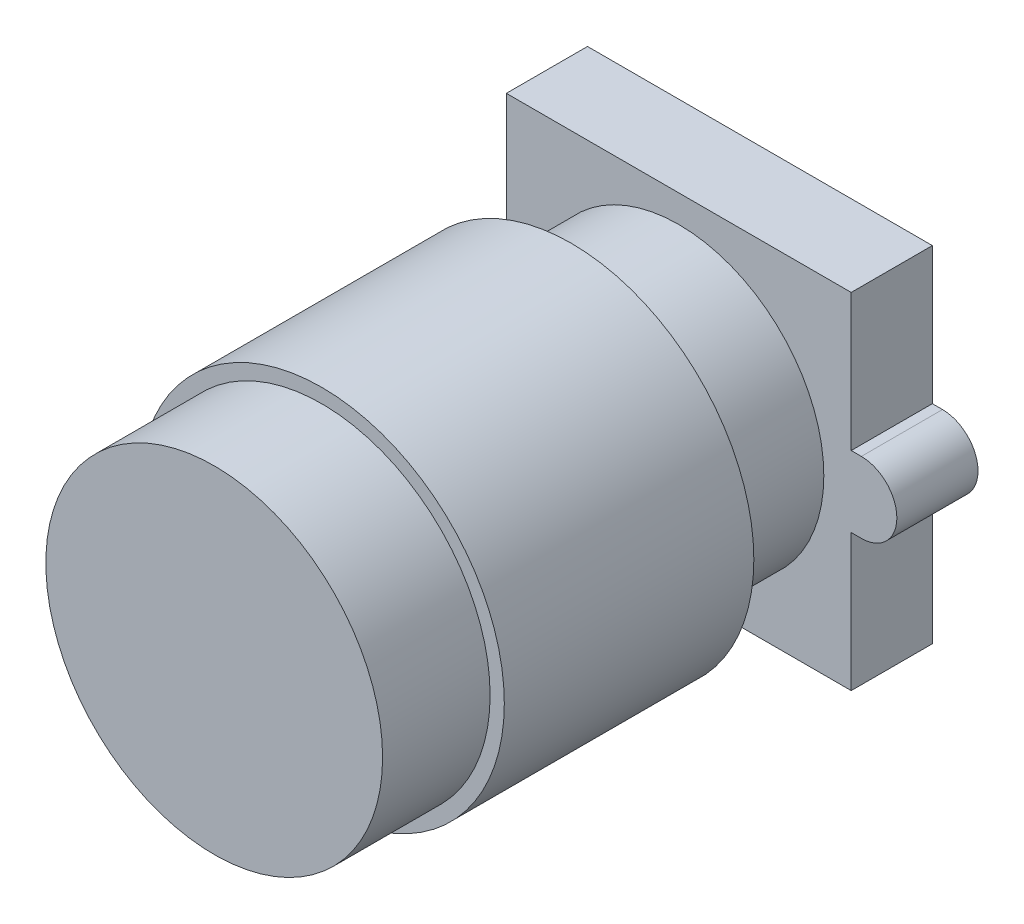
SolidWorks part; units mm, degrees
ref_plane "Front Plane" through (0, 0, 0) normal (0, 0, 1) x (1, 0, 0)
ref_plane "Top Plane" through (0, 0, 0) normal (0, 1, 0) x (1, 0, 0)
ref_plane "Right Plane" through (0, 0, 0) normal (1, 0, 0) x (0, 0, -1)
sketch "Sketch2" plane through (0, 0, 0) normal (0, 0, 1) x (1, 0, 0)
  line L0 (-9, 0) -> (9, 0) construction
  line L1 (8.5, -8.5) -> (-8.5, -8.5)
  line L2 (8.5, -8.5) -> (8.5, 8.5)
  line L3 (8.5, 8.5) -> (-8.5, 8.5)
  line L4 (-8.5, -8.5) -> (-8.5, 8.5)
  line L5 (8.5, -8.5) -> (-8.5, 8.5) construction
  line L6 (8.5, 8.5) -> (-8.5, -8.5) construction
  line L7 (-9, 1.75) -> (9, 1.75)
  line L8 (-9, -1.75) -> (9, -1.75)
  arc A0 (-9, 1.75) -> (-9, -1.75) centre (-9, 0) ccw
  arc A1 (9, -1.75) -> (9, 1.75) centre (9, 0) ccw
  point P0 (0, 0)
  point P8 (0, 0)
  point P13 (0, 0)
  dimension "D3" = 21.5
  dimension "D4" = 1.75
  dimension "D1" = 17
  dimension "D2" = 17
extrude "Boss-Extrude1" add sketch "Sketch2" along normal blind 4 contours L4 L8 L2 L7 | L7 A0 L8 L4 | L4 L7 L2 L3 | L8 L4 L1 L2 | L8 A1 L7 L2
sketch "Sketch3" plane through (0, 0, 4) normal (0, 0, 1) x (1, 0, 0)
  circle A0 centre (0, 0) radius 7.15
  point P3 (0, 0)
  dimension "D1" = 14.3
extrude "Boss-Extrude2" add sketch "Sketch3" along normal blind 5.3
sketch "Sketch4" plane through (0, 0, 9.3) normal (0, 0, 1) x (1, 0, 0)
  circle A0 centre (0, 0) radius 9
  dimension "D1" = 18
extrude "Boss-Extrude3" add sketch "Sketch4" along normal blind 12.3
sketch "Sketch5" plane through (0, 0, 21.6) normal (0, 0, 1) x (1, 0, 0)
  circle A0 centre (0, 0) radius 8.3
  dimension "D1" = 16.6
extrude "Boss-Extrude4" add sketch "Sketch5" along normal blind 5.3
